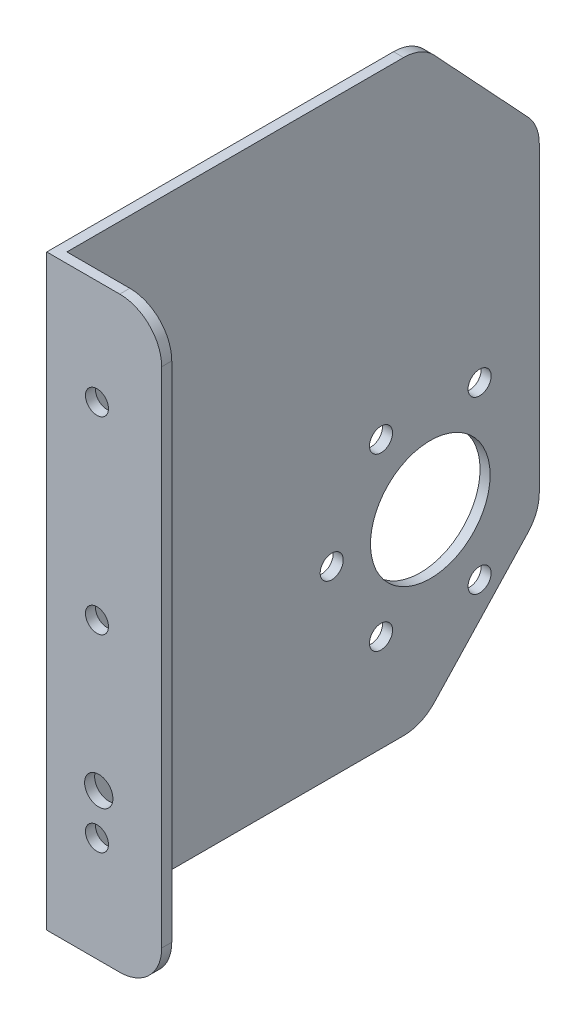
SolidWorks part; units mm, degrees
ref_plane "Front Plane" through (0, 0, 0) normal (0, 0, 1) x (1, 0, 0)
ref_plane "Top Plane" through (0, 0, 0) normal (0, 1, 0) x (1, 0, 0)
ref_plane "Right Plane" through (0, 0, 0) normal (1, 0, 0) x (0, 0, -1)
sketch "Sketch1" plane through (0, 0, 0) normal (1, 0, 0) x (0, 0, -1)
  line L1 (0, 0) -> (115, 0)
  line L2 (0, 0) -> (0, -140)
  line L3 (0, -140) -> (115, -140)
  line L4 (115, 0) -> (115, -140)
  dimension "D1" = 115
  dimension "D2" = 140
extrude "Boss-Extrude1" add sketch "Sketch1" along normal blind 2.4
sketch "Sketch2" plane through (2.4, 0, 0) normal (1, 0, 0) x (0, 0, -1)
  line L0 (87, 0) -> (115, -30)
  line L1 (115, 0) -> (0, 0) construction
  line L2 (115, -140) -> (115, 0) construction
  line L3 (115, -30) -> (142.6162, -32.5054)
  line L4 (142.6162, -32.5054) -> (142.6162, 14.8756)
  line L5 (142.6162, 14.8756) -> (87, 0)
  line L6 (115, -110) -> (87, -140)
  line L7 (0, -140) -> (115, -140) construction
  line L8 (87, -140) -> (87, -152.6611)
  line L9 (87, -152.6611) -> (136.31, -152.6611)
  line L10 (136.31, -152.6611) -> (115, -110)
  line L12 (0, 0) -> (0, -140) construction
  dimension "D1" = 30
  dimension "D2" = 87
  dimension "D3" = 87
  dimension "D4" = 30
extrude "Cut-Extrude1" cut sketch "Sketch2" against normal through all
fillet "Fillet1" radius 10 4 edges at (1.2, -140, -87) (1.2, -110, -115) (1.2, -30, -115) (1.2, 0, -87)
sketch "Sketch3" plane through (2.4, 0, 0) normal (1, 0, 0) x (0, 0, -1)
  line L0 (82.6545, 0) -> (0, 0) construction
  line L1 (0, -140) -> (2.4, -140)
  line L2 (0, -140) -> (0, 0)
  line L3 (0, 0) -> (2.4, 0)
  line L4 (2.4, -140) -> (2.4, 0)
  dimension "D1" = 2.4
extrude "Boss-Extrude2" add sketch "Sketch3" along normal blind 25
fillet "Fillet2" radius 10 2 edges at (27.4, -140, -1.2) (27.4, 0, -1.2)
sketch "Sketch4" plane through (0, 0, 0) normal (0, 0, 1) x (1, 0, 0)
  line L0 (17.4, 0) -> (0, 0) construction
  line L1 (17.4, -140) -> (0, -140) construction
  line L2 (27.4, -10) -> (27.4, -130) construction
  circle A0 centre (11.975, -70) radius 2.75
  circle A1 centre (11.975, -25) radius 2.75
  circle A2 centre (11.975, -115) radius 2.75
  point P12 (27.4, -70)
  dimension "D1" = 5.5
  dimension "D2" = 5.5
  dimension "D3" = 5.5
  dimension "D4" = 25
  dimension "D5" = 25
extrude "Cut-Extrude2" cut sketch "Sketch4" against normal through all
sketch "Sketch5" plane through (2.4, 0, 0) normal (1, 0, 0) x (0, 0, -1)
  circle A2 centre (89.0279, -96.494) radius 14.26 construction
  circle A13 centre (89.0279, -96.494) radius 14.26
  circle A14 centre (77.2779, -76.1424) radius 2.75 construction
  circle A15 centre (77.2779, -76.1424) radius 2.75
  circle A16 centre (100.7779, -76.1424) radius 2.75 construction
  circle A17 centre (100.7779, -76.1424) radius 2.75
  circle A20 centre (100.7779, -116.8456) radius 2.75 construction
  circle A21 centre (100.7779, -116.8456) radius 2.75
  circle A22 centre (77.2779, -116.8456) radius 2.75 construction
  circle A23 centre (77.2779, -116.8456) radius 2.75
  circle A24 centre (65.5279, -96.494) radius 2.75 construction
  circle A25 centre (65.5279, -96.494) radius 2.75
extrude "Cut-Extrude3" cut sketch "Sketch5" against normal through all
sketch "Sketch6" plane through (0, 0, 0) normal (0, 0, 1) x (1, 0, 0)
  circle A0 centre (12.4, -105) radius 3.375 construction
  circle A1 centre (12.4, -105) radius 3.375
extrude "Cut-Extrude4" cut sketch "Sketch6" against normal through all
